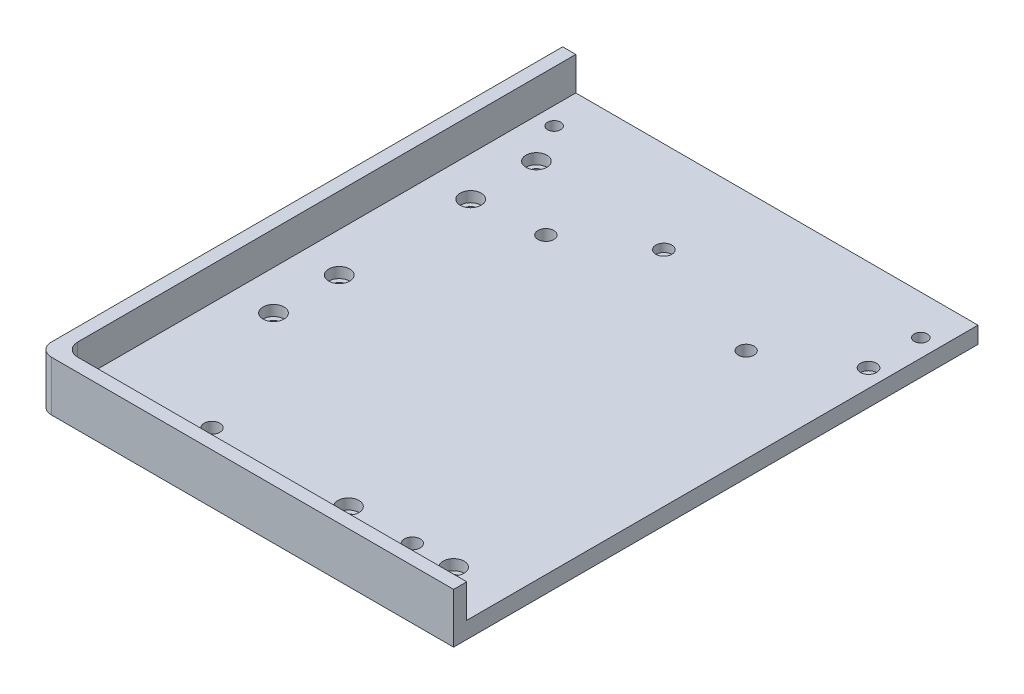
SolidWorks part; units mm, degrees
ref_plane "Front Plane" through (0, 0, 0) normal (0, 0, 1) x (1, 0, 0)
ref_plane "Top Plane" through (0, 0, 0) normal (0, 1, 0) x (1, 0, 0)
ref_plane "Right Plane" through (0, 0, 0) normal (1, 0, 0) x (0, 0, -1)
sketch "Sketch1" plane through (0, 0, 0) normal (0, 1, 0) x (1, 0, 0)
  line L1 (0, 0) -> (158, 0)
  line L2 (0, 0) -> (0, -199.5)
  line L3 (0, -199.5) -> (158, -199.5)
  line L4 (158, 0) -> (158, -199.5)
  dimension "D1" = 158
  dimension "D2" = 199.5
extrude "Boss-Extrude1" add sketch "Sketch1" along normal blind 6.35
sketch "Sketch2" [suppressed] plane through (0, 6.35, 0) normal (0, 1, 0) x (1, 0, 0)
  line L0 (0, -199.5) -> (158, -199.5) construction
  line L1 (81, -199.5) -> (0, -199.5)
  line L2 (81, -199.5) -> (81, -158.5)
  line L3 (81, -158.5) -> (0, -158.5)
  line L4 (0, -199.5) -> (0, -158.5)
  dimension "D1" = 81
  dimension "D2" = 41
sketch "Sketch3" plane through (0, 6.35, 0) normal (0, 1, 0) x (1, 0, 0)
  line L22 (0, 0) -> (0, -199.5) construction
  line L30 (0, -199.5) -> (158, -199.5) construction
  line L34 (0, 0) -> (0, -199.5)
  line L35 (0, -199.5) -> (158, -199.5)
  line L36 (5, 0) -> (5, -194.5)
  line L37 (5, -194.5) -> (158, -194.5)
  line L38 (158, -199.5) -> (158, -194.5)
  line L39 (0, 0) -> (5, 0)
  dimension "D1" = 5
extrude "Boss-Extrude2" add sketch "Sketch3" along normal blind 12.7
sketch "Sketch4" plane through (0, 6.35, 0) normal (0, -1, 0) x (1, 0, 0)
  line L0 (78, 179.5) -> (158, 179.5) construction
  line L3 (0, 199.5) -> (158, 199.5) construction
  line L4 (118, 179.5) -> (118, 188.5903) construction
  line L5 (20, 160) -> (20, 0) construction
  line L7 (158, 0) -> (0, 0) construction
  line L9 (20, 80) -> (152.6176, 80) construction
  line L10 (158, 199.5) -> (158, 0) construction
  line L12 (0, 0) -> (0, 199.5) construction
  point P8 (98, 179.5)
  point P11 (138, 179.5)
  point P20 (20, 130)
  point P21 (20, 105)
  point P22 (20, 30)
  point P23 (20, 80)
  point P24 (20, 55)
  dimension "D1" = 20
  dimension "D2" = 40
  dimension "D3" = 20
  dimension "D4" = 25
  dimension "D5" = 25
  dimension "D6" = 160
  dimension "D7" = 80
hole_wizard "CBORE for M4 SHCS1" positions "Sketch4" profile "Sketch5" counterbore size "M4" standard "ANSI Metric" end condition up to next
sketch "Sketch5" plane through (20, 6.35, 55) normal (1, 0, 0) x (0, 0, 1)
  line L0 (0, 0) -> (0, 6.35)
  line L1 (0, 6.35) -> (2.25, 6.35)
  line L3 (2.25, 6.35) -> (2.25, 4)
  line L4 (2.25, 4) -> (4, 4)
  line L5 (4, 4) -> (4, 0)
  line L7 (4, 0) -> (0, 0)
  line L11 (0, -6.35) -> (0, 107.95) construction
  dimension "Thru Hole Dia." = 4.5
  dimension "Thru Hole Depth" = 6.35
  dimension "C'Bore Dia." = 8
  dimension "C'Bore Depth" = 4
sketch "Sketch7" [suppressed] plane through (0, 0, 0) normal (0, 0, -1) x (-1, 0, 0)
  line L0 (-79, 19.05) -> (-79, 4.7647) construction
  line L2 (-158, 19.05) -> (0, 19.05) construction
  line L3 (-158, 19.05) -> (-29, 19.05)
  line L4 (-158, 19.05) -> (-158, 9.05)
  line L5 (-158, 9.05) -> (-29, 9.05)
  line L6 (-29, 19.05) -> (-29, 9.05)
  line L7 (0, 19.05) -> (0, 0) construction
  line L8 (-158, 6.35) -> (-158, 0) construction
  dimension "D1" = 29
  dimension "D2" = 10
extrude "Cut-Extrude2" [suppressed] cut sketch "Sketch7" against normal up to next
fillet "Fillet1" [suppressed] radius 5
fillet "Fillet2" radius 5 2 edges at (5, 12.7, 194.5) (0, 9.525, 199.5)
sketch "Sketch8" plane through (0, 6.35, 0) normal (0, 1, 0) x (1, 0, 0)
  line L1 (122.3, -179.5) -> (46.1, -179.5) construction
  line L2 (122.3, -179.5) -> (122.3, -52.5) construction
  line L3 (122.3, -52.5) -> (46.1, -52.5) construction
  line L4 (46.1, -179.5) -> (46.1, -52.5) construction
  line L5 (122.3, -179.5) -> (46.1, -52.5) construction
  line L6 (122.3, -52.5) -> (46.1, -179.5) construction
  line L7 (5, -189.5) -> (5, 0) construction
  line L8 (158, -194.5) -> (10, -194.5) construction
  circle A0 centre (46.1, -52.5) radius 3
  circle A1 centre (122.3, -52.5) radius 3
  circle A2 centre (122.3, -179.5) radius 3
  circle A3 centre (46.1, -179.5) radius 3
  point P0 (84.2, -116)
  dimension "D1" = 6
  dimension "D2" = 76.2
  dimension "D3" = 127
  dimension "D4" = 41.1
  dimension "D5" = 15
extrude "Enclosure Mount" cut sketch "Sketch8" against normal through all
sketch "Sketch9" plane through (0, 6.35, 0) normal (0, 1, 0) x (1, 0, 0)
  line L0 (11.75, -15) -> (151.25, -15) construction
  line L2 (158, 0) -> (5, 0) construction
  circle A0 centre (11.75, -15) radius 2.5
  circle A1 centre (151.25, -15) radius 2.5
  point P4 (81.5, 0)
  point P5 (81.5, -15)
  dimension "D1" = 5
  dimension "D2" = 139.5
  dimension "D4" = 15
extrude "Fuse Mount" cut sketch "Sketch9" against normal through all
sketch "Sketch10" plane through (0, 6.35, 0) normal (0, 1, 0) x (1, 0, 0)
  line L0 (158, 0) -> (5, 0) construction
  circle A0 centre (151.25, -34.9) radius 3.05
  circle A1 centre (73.375, -34.9) radius 3.05
  point P4 (151.25, -15)
  point P8 (73.375, -34.9)
  dimension "D2" = 6.1
  dimension "D1" = 34.9
  dimension "D3" = 77.875
extrude "Magnets" cut sketch "Sketch10" against normal blind 3.1
equation "\"D4@Sketch8\"=38.1+3"
equation "\"D5@Sketch8\"=12.7+2.3"
